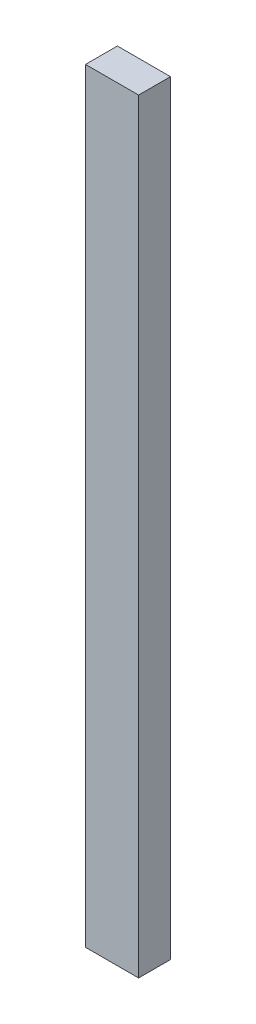
SolidWorks part; units mm, degrees
ref_plane "Front Plane" through (0, 0, 0) normal (0, 0, 1) x (1, 0, 0)
ref_plane "Top Plane" through (0, 0, 0) normal (0, 1, 0) x (1, 0, 0)
ref_plane "Right Plane" through (0, 0, 0) normal (1, 0, 0) x (0, 0, -1)
sketch "Sketch1" plane through (0, 0, 0) normal (0, 1, 0) x (1, 0, 0)
  line L1 (-31.75, -19.05) -> (31.75, -19.05)
  line L2 (-31.75, -19.05) -> (-31.75, 19.05)
  line L3 (-31.75, 19.05) -> (31.75, 19.05)
  line L4 (31.75, -19.05) -> (31.75, 19.05)
  line L5 (-31.75, -19.05) -> (31.75, 19.05) construction
  line L6 (-31.75, 19.05) -> (31.75, -19.05) construction
  point P0 (0, 0)
  dimension "D1" = 38.1
  dimension "D2" = 63.5
extrude "Boss-Extrude1" add sketch "Sketch1" along normal blind 914.4
